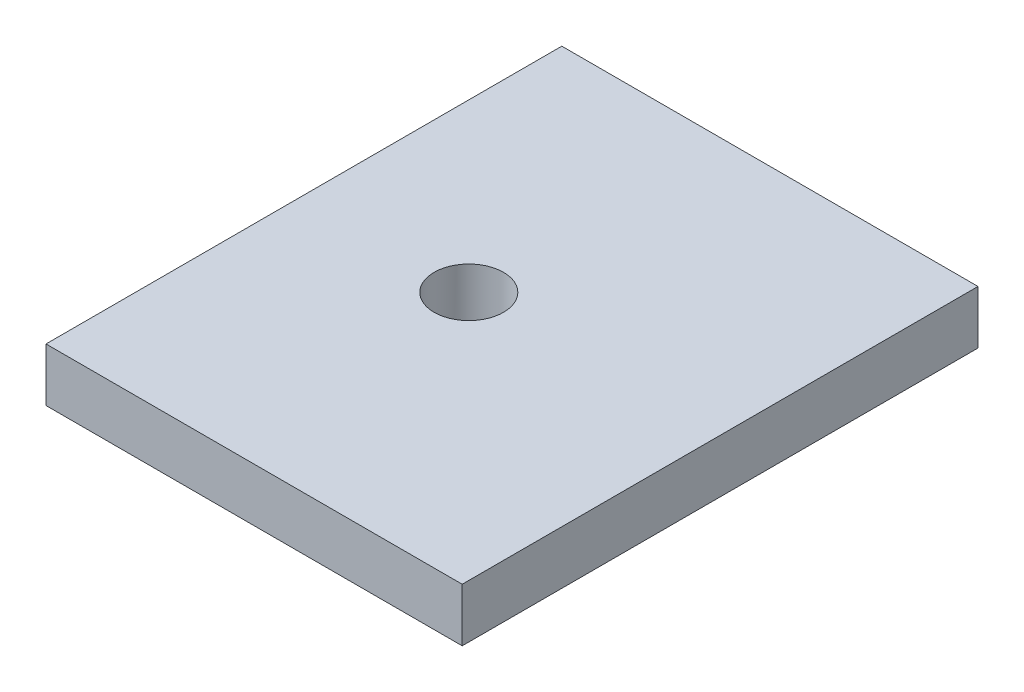
SolidWorks part; units mm, degrees
material "Custom Plastic"
ref_plane "Front Plane" through (0, 0, 0) normal (0, 0, 1) x (1, 0, 0)
ref_plane "Top Plane" through (0, 0, 0) normal (0, 1, 0) x (1, 0, 0)
ref_plane "Right Plane" through (0, 0, 0) normal (1, 0, 0) x (0, 0, -1)
sketch "Sketch1" plane through (0, 0, 0) normal (0, 1, 0) x (1, 0, 0)
  line L0 (-30.4611, 0) -> (33.997, 0) construction
  line L1 (-11.7, -14.5) -> (11.7, -14.5)
  line L2 (-11.7, -14.5) -> (-11.7, 14.5)
  line L3 (-11.7, 14.5) -> (11.7, 14.5)
  line L4 (11.7, -14.5) -> (11.7, 14.5)
  line L5 (-11.7, -14.5) -> (11.7, 14.5) construction
  line L6 (-11.7, 14.5) -> (11.7, -14.5) construction
  circle A0 centre (9, 8.9) radius 1
  circle A2 centre (9, -8.5) radius 1
  circle A3 centre (-9, -8.5) radius 1
  circle A5 centre (1.7, -8.5) radius 1
  spline S1 degree 3 poles (19.181, -14.2425) (19.8008, -12.3411) (17.8993, -11.7212) (17.2795, -13.6227) (16.6596, -15.5241) (18.5612, -16.144) (19.181, -14.2425) (19.8008, -12.3411) (17.8993, -11.7212) knots -0.5 0 0 0 0.5 0.5 0.5 1 1 1 1.5 1.5 1.5 weights 1 0.333333 0.333333 1 0.333333 0.333333 1 0.333333 0.333333 only from (19.181, -14.2425) to (19.181, -14.2425) construction
  spline S2 degree 3 poles (22.4885, -4.0962) (23.1083, -2.1947) (21.2068, -1.5749) (20.587, -3.4763) (19.9671, -5.3778) (21.8687, -5.9977) (22.4885, -4.0962) (23.1083, -2.1947) (21.2068, -1.5749) knots -0.5 0 0 0 0.5 0.5 0.5 1 1 1 1.5 1.5 1.5 weights 1 0.333333 0.333333 1 0.333333 0.333333 1 0.333333 0.333333 only from (22.4885, -4.0962) to (22.4885, -4.0962) construction
  spline S3 degree 3 poles (19.181, -14.2425) (19.8008, -12.3411) (17.8993, -11.7212) (17.2795, -13.6227) (16.6596, -15.5241) (18.5612, -16.144) (19.181, -14.2425) (19.8008, -12.3411) (17.8993, -11.7212) knots -0.5 0 0 0 0.5 0.5 0.5 1 1 1 1.5 1.5 1.5 weights 1 0.333333 0.333333 1 0.333333 0.333333 1 0.333333 0.333333 only from (19.181, -14.2425) to (19.181, -14.2425)
  spline S4 degree 3 poles (22.4885, -4.0962) (23.1083, -2.1947) (21.2068, -1.5749) (20.587, -3.4763) (19.9671, -5.3778) (21.8687, -5.9977) (22.4885, -4.0962) (23.1083, -2.1947) (21.2068, -1.5749) knots -0.5 0 0 0 0.5 0.5 0.5 1 1 1 1.5 1.5 1.5 weights 1 0.333333 0.333333 1 0.333333 0.333333 1 0.333333 0.333333 only from (22.4885, -4.0962) to (22.4885, -4.0962)
  point P0 (0, 0)
  point P6 (-9, 8.5)
  point P7 (9, 8.5)
  point P8 (9, 8.9)
  point P18 (1.7, 8.5)
  dimension "D7" = 17.4
  dimension "D8" = 18
  dimension "D10" = 2
  dimension "D1" = 29
  dimension "D2" = 23.4
  dimension "D3" = 6
  dimension "D4" = 6
  dimension "D5" = 18
  dimension "D6" = 2.7
  dimension "D9" = 10.7
extrude "Boss-Extrude1" add sketch "Sketch1" along normal blind 3
sketch "Sketch5" plane through (0, 0, 0) normal (0, -1, 0) x (1, 0, 0)
  circle A0 centre (-2.1456, 3.6104) radius 2.5 construction
  circle A1 centre (-2.1456, 3.6104) radius 2.5 construction
  circle A2 centre (-2.1456, 3.6104) radius 1.44
  dimension "D1" = 2.88
extrude "Cut-Extrude3" cut sketch "Sketch5" against normal blind 10
sketch "Sketch7" plane through (0, 3, 0) normal (0, 1, 0) x (1, 0, 0)
  spline S0 degree 3 poles (19.181, -14.2425) (19.8008, -12.3411) (17.8993, -11.7212) (17.2795, -13.6227) (16.6596, -15.5241) (18.5612, -16.144) (19.181, -14.2425) (19.8008, -12.3411) (17.8993, -11.7212) knots -0.5 0 0 0 0.5 0.5 0.5 1 1 1 1.5 1.5 1.5 weights 1 0.333333 0.333333 1 0.333333 0.333333 1 0.333333 0.333333 only from (19.181, -14.2425) to (19.181, -14.2425) construction
  spline S1 degree 3 poles (22.4885, -4.0962) (23.1083, -2.1947) (21.2068, -1.5749) (20.587, -3.4763) (19.9671, -5.3778) (21.8687, -5.9977) (22.4885, -4.0962) (23.1083, -2.1947) (21.2068, -1.5749) knots -0.5 0 0 0 0.5 0.5 0.5 1 1 1 1.5 1.5 1.5 weights 1 0.333333 0.333333 1 0.333333 0.333333 1 0.333333 0.333333 only from (22.4885, -4.0962) to (22.4885, -4.0962) construction
  spline S2 degree 3 poles (19.181, -14.2425) (19.8008, -12.3411) (17.8993, -11.7212) (17.2795, -13.6227) (16.6596, -15.5241) (18.5612, -16.144) (19.181, -14.2425) (19.8008, -12.3411) (17.8993, -11.7212) knots -0.5 0 0 0 0.5 0.5 0.5 1 1 1 1.5 1.5 1.5 weights 1 0.333333 0.333333 1 0.333333 0.333333 1 0.333333 0.333333 only from (19.181, -14.2425) to (19.181, -14.2425)
  spline S3 degree 3 poles (22.4885, -4.0962) (23.1083, -2.1947) (21.2068, -1.5749) (20.587, -3.4763) (19.9671, -5.3778) (21.8687, -5.9977) (22.4885, -4.0962) (23.1083, -2.1947) (21.2068, -1.5749) knots -0.5 0 0 0 0.5 0.5 0.5 1 1 1 1.5 1.5 1.5 weights 1 0.333333 0.333333 1 0.333333 0.333333 1 0.333333 0.333333 only from (22.4885, -4.0962) to (22.4885, -4.0962)
extrude "Cut-Extrude4" cut sketch "Sketch7" against normal blind 10
sketch "Sketch8" plane through (0, 3, 0) normal (0, 1, 0) x (1, 0, 0)
  line L0 (24.633, 0) -> (-21.7502, 0) construction
  line L1 (1.7, -8.5) -> (1.7, 20.7764) construction
  line L2 (-9, -8.5) -> (-9, 21.3011) construction
  line L3 (9, -8.5) -> (9, 8.9) construction
  line L4 (14.3582, 8.9) -> (-23.7207, 8.9) construction
  circle A0 centre (1.7, 8.9) radius 1
  circle A1 centre (-9, 8.9) radius 1
  point P15 (1.7, 8.9)
  point P16 (-9, 8.9)
  dimension "D1" = 2
  dimension "D2" = 2
extrude "Cut-Extrude5" cut sketch "Sketch8" against normal blind 10
sketch "Sketch9" plane through (0, 3, 0) normal (0, 1, 0) x (1, 0, 0)
  circle A0 centre (-2.1456, -3.6104) radius 3.027
extrude "Boss-Extrude3" add sketch "Sketch9" against normal up to surface (3 mm away) up to face at (-9, 0, -9.9)
sketch "Sketch10" plane through (0, 3, 0) normal (0, 1, 0) x (1, 0, 0)
  circle A1 centre (-2.3282, -0.1) radius 1.5 construction
  circle A2 centre (-2.3282, -0.1) radius 1.95
  circle A3 centre (-2.3282, -0.1) radius 4 construction
  dimension "D1" = 3.9
extrude "Cut-Extrude6" cut sketch "Sketch10" against normal blind 10
sketch "Sketch11" plane through (0, 3, 0) normal (0, 1, 0) x (1, 0, 0)
  line L4 (11.7, -14.5) -> (11.7, 14.5)
  line L5 (11.7, 14.5) -> (-11.7, 14.5)
  line L6 (-11.7, 14.5) -> (-11.7, -14.5)
  line L7 (-11.7, -14.5) -> (11.7, -14.5)
  line L8 (11.7, -14.5) -> (11.7, 14.5)
  line L9 (11.7, 14.5) -> (-11.7, 14.5)
  line L10 (-11.7, 14.5) -> (-11.7, -14.5)
  line L11 (-11.7, -14.5) -> (11.7, -14.5)
  circle A0 centre (-2.3282, -0.1) radius 1.95 construction
  circle A1 centre (-2.3282, -0.1) radius 1.95
  dimension "D1" = 0
extrude "Boss-Extrude4" add sketch "Sketch11" against normal up to surface (3 mm away) up to face at (-2.3282, 0, -1.85)
